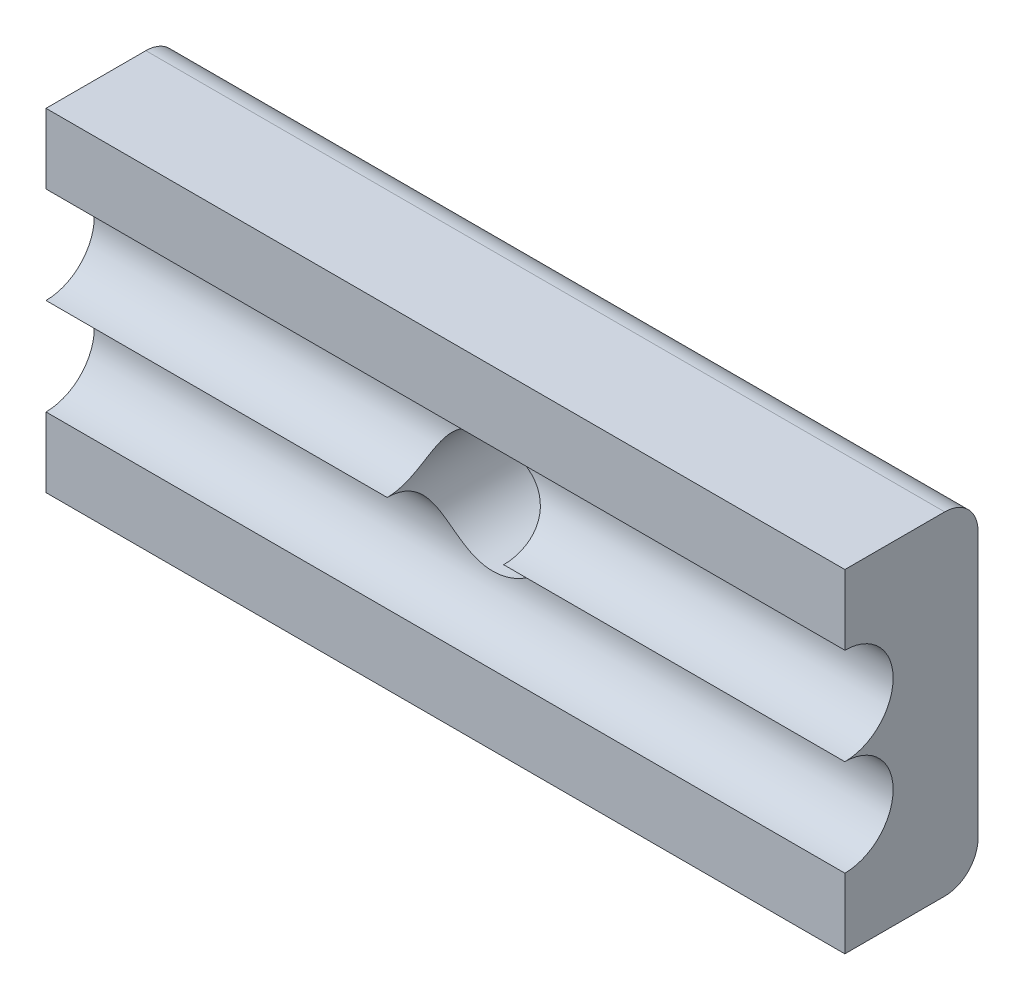
SolidWorks part; units mm, degrees
ref_plane "Front Plane" through (0, 0, 0) normal (0, 0, 1) x (1, 0, 0)
ref_plane "Top Plane" through (0, 0, 0) normal (0, 1, 0) x (1, 0, 0)
ref_plane "Right Plane" through (0, 0, 0) normal (1, 0, 0) x (0, 0, -1)
sketch "Sketch2" plane through (0, 0, 0) normal (0, 0, 1) x (1, 0, 0)
  line L1 (-5.0427, 4) -> (18.9573, 4)
  line L2 (-5.0427, 4) -> (-5.0427, -6)
  line L3 (-5.0427, -6) -> (18.9573, -6)
  line L4 (18.9573, 4) -> (18.9573, -6)
  dimension "D1" = 10
  dimension "D2" = 24
extrude "Boss-Extrude1" add sketch "Sketch2" along normal blind 4
sketch "Sketch3" plane through (0, 0, 4) normal (0, 0, 1) x (1, 0, 0)
  line L0 (-5.0427, 4) -> (-5.0427, -6) construction
  line L1 (18.9573, 4) -> (-5.0427, 4) construction
  circle A0 centre (6.9573, -1) radius 1.75
  point P5 (-5.0427, -1)
  point P8 (6.9573, 4)
  dimension "D1" = 3.5
extrude "Cut-Extrude1" cut sketch "Sketch3" against normal blind 5
sketch "Sketch4" plane through (-5.0427, 0, 0) normal (-1, 0, 0) x (0, 0, 1)
  line L1 (4, 4) -> (4, -6) construction
  line L2 (0, 4) -> (0, -6) construction
  circle A0 centre (4, -2.45) radius 1.45
  circle A2 centre (4, 0.45) radius 1.45
  point P10 (0, -1)
  point P15 (4, -1)
  line M4 (4, -6) -> (4, 4)
  dimension "D1" = 2.9
  dimension "D2" = 2.9
fillet "Fillet1" radius 1 2 edges at (6.9573, -6, 0) (6.9573, 4, 0)
extrude "Cut-Extrude2" cut sketch "Sketch4" against normal blind 30 contours A0 M4 | A2 M4
